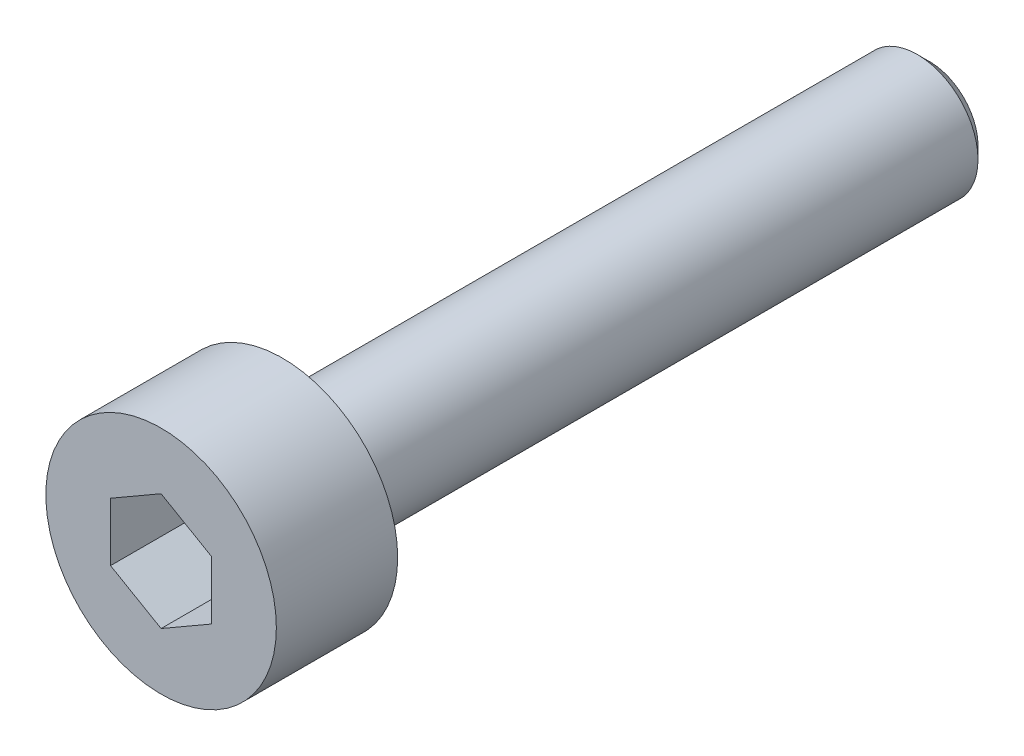
SolidWorks part; units mm, degrees
ref_plane "Front Plane" through (0, 0, 0) normal (0, 0, 1) x (1, 0, 0)
ref_plane "Top Plane" through (0, 0, 0) normal (0, 1, 0) x (1, 0, 0)
ref_plane "Right Plane" through (0, 0, 0) normal (1, 0, 0) x (0, 0, -1)
sketch "Sketch1" plane through (0, 0, 0) normal (0, 0, 1) x (1, 0, 0)
  circle A0 centre (0, 0) radius 2.85
  dimension "D1" = 5.7
extrude "Boss-Extrude1" add sketch "Sketch1" along normal blind 3
sketch "Sketch2" plane through (0, 0, 0) normal (0, 0, -1) x (-1, 0, 0)
  circle A0 centre (0, 0) radius 1.5
  dimension "D1" = 3
extrude "Boss-Extrude2" add sketch "Sketch2" along normal blind 16
chamfer "Chamfer1" distance 0.3 angle 45 1 edges at (-1.5, 0, -16)
sketch "Sketch3" plane through (0, 0, 3) normal (0, 0, 1) x (1, 0, 0)
  line L1 (0, 1.4434) -> (-1.25, 0.7217)
  line L2 (-1.25, 0.7217) -> (-1.25, -0.7217)
  line L3 (-1.25, -0.7217) -> (0, -1.4434)
  line L4 (0, -1.4434) -> (1.25, -0.7217)
  line L5 (1.25, -0.7217) -> (1.25, 0.7217)
  line L6 (1.25, 0.7217) -> (0, 1.4434)
  circle A0 centre (0, 0) radius 1.25 construction
  dimension "D1" = 2.5
extrude "Cut-Extrude1" cut sketch "Sketch3" against normal blind 2
